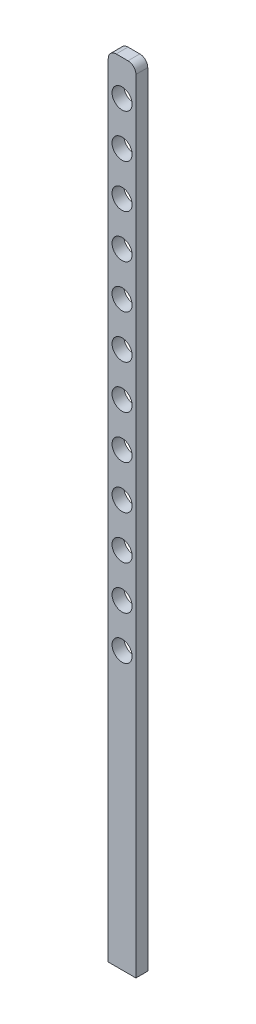
SolidWorks part; units mm, degrees
ref_plane "Front Plane" through (0, 0, 0) normal (0, 0, 1) x (1, 0, 0)
ref_plane "Top Plane" through (0, 0, 0) normal (0, 1, 0) x (1, 0, 0)
ref_plane "Right Plane" through (0, 0, 0) normal (1, 0, 0) x (0, 0, -1)
sketch "Sketch1" plane through (0, 0, 0) normal (0, 0, 1) x (1, 0, 0)
  line L1 (-17.5, 500) -> (17.5, 500)
  line L2 (-17.5, 500) -> (-17.5, -500)
  line L3 (-17.5, -500) -> (17.5, -500)
  line L4 (17.5, 500) -> (17.5, -500)
  line L5 (-17.5, 500) -> (17.5, -500) construction
  line L6 (-17.5, -500) -> (17.5, 500) construction
  point P0 (0, 0)
  dimension "D1" = 1000
  dimension "D2" = 35
extrude "Boss-Extrude1" add sketch "Sketch1" along normal mid plane 15
sketch "Sketch2" plane through (0, 0, 0) normal (0, 0, 1) x (1, 0, 0)
  circle A0 centre (0, -150) radius 12.7
  dimension "D1" = 25.4
  dimension "D2" = 150
extrude "Cut-Extrude1" cut sketch "Sketch2" against normal through all both and the other way through all
pattern_linear "LPattern1" count 12 spacing 55 along (0, 1, 0) of "Cut-Extrude1"
fillet "Fillet1" radius 10 2 edges at (17.5, 500, 0) (-17.5, 500, 0)
